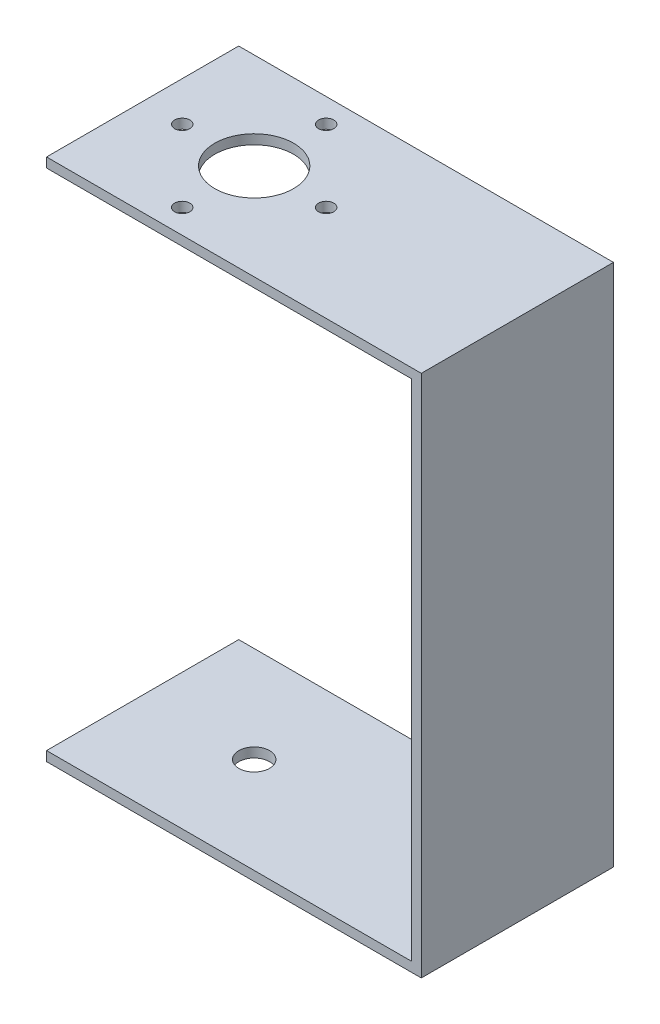
SolidWorks part; units mm, degrees
ref_plane "正面" through (0, 0, 0) normal (0, 0, 1) x (1, 0, 0)
ref_plane "平面" through (0, 0, 0) normal (0, 1, 0) x (1, 0, 0)
ref_plane "右側面" through (0, 0, 0) normal (1, 0, 0) x (0, 0, -1)
sketch "ｽｹｯﾁ1" plane through (0, 0, 0) normal (1, 0, 0) x (0, 0, -1)
  line L1 (0, 0) -> (20, 0)
  line L2 (0, 0) -> (0, 54.5)
  line L3 (0, 54.5) -> (20, 54.5)
  line L4 (20, 0) -> (20, 54.5)
extrude "ﾎﾞｽ - 押し出し1" add sketch "ｽｹｯﾁ1" along normal blind 1
sketch "ｽｹｯﾁ2" plane through (0, 0, 0) normal (-1, 0, 0) x (0, 0, 1)
  line L0 (0, 54.5) -> (0, 0) construction
  line L1 (-20, 54.5) -> (0, 54.5)
  line L2 (-20, 54.5) -> (-20, 53.5)
  line L3 (-20, 53.5) -> (0, 53.5)
  line L4 (0, 54.5) -> (0, 53.5)
extrude "ﾎﾞｽ - 押し出し2" add sketch "ｽｹｯﾁ2" along normal blind 38
sketch "ｽｹｯﾁ3" plane through (0, 0, 0) normal (-1, 0, 0) x (0, 0, 1)
  line L0 (-20, 0) -> (-20, 53.5) construction
  line L1 (0, 0) -> (-20, 0)
  line L2 (0, 0) -> (0, 1)
  line L3 (0, 1) -> (-20, 1)
  line L4 (-20, 0) -> (-20, 1)
extrude "ﾎﾞｽ - 押し出し3" add sketch "ｽｹｯﾁ3" along normal blind 38
sketch "ｽｹｯﾁ4" plane through (0, 54.5, 0) normal (0, 1, 0) x (1, 0, 0)
  circle A0 centre (-26.39, 10) radius 4.1
extrude "ｶｯﾄ - 押し出し1" cut sketch "ｽｹｯﾁ4" against normal blind 1
sketch "ｽｹｯﾁ5" plane through (0, 54.5, 0) normal (0, 1, 0) x (1, 0, 0)
  circle A0 centre (-33.88, 10) radius 0.79
extrude "ｶｯﾄ - 押し出し2" cut sketch "ｽｹｯﾁ5" against normal blind 1
sketch "ｽｹｯﾁ6" plane through (0, 54.5, 0) normal (0, 1, 0) x (1, 0, 0)
  circle A0 centre (-18.9, 10) radius 0.79
extrude "ｶｯﾄ - 押し出し3" cut sketch "ｽｹｯﾁ6" against normal blind 1
sketch "ｽｹｯﾁ7" plane through (0, 54.5, 0) normal (0, 1, 0) x (1, 0, 0)
  circle A0 centre (-26.39, 2.51) radius 0.79
extrude "ｶｯﾄ - 押し出し4" cut sketch "ｽｹｯﾁ7" against normal blind 1
sketch "ｽｹｯﾁ8" plane through (0, 54.5, 0) normal (0, 1, 0) x (1, 0, 0)
  circle A0 centre (-26.39, 17.49) radius 0.79
extrude "ｶｯﾄ - 押し出し5" cut sketch "ｽｹｯﾁ8" against normal blind 1
sketch "ｽｹｯﾁ9" plane through (0, 0, 0) normal (0, -1, 0) x (-1, 0, 0)
  circle A0 centre (26.39, 10) radius 1.6
extrude "ｶｯﾄ - 押し出し6" cut sketch "ｽｹｯﾁ9" against normal blind 1
